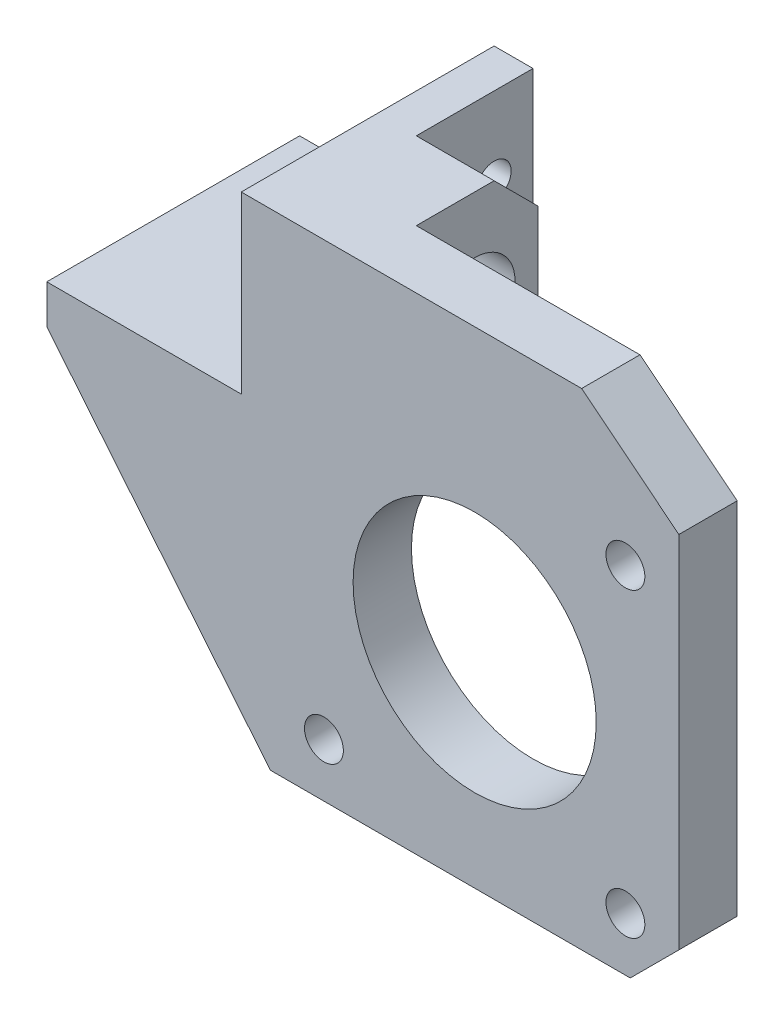
SolidWorks part; units mm, degrees
ref_plane "Plano frontal" through (0, 0, 0) normal (0, 0, 1) x (1, 0, 0)
ref_plane "Plano superior" through (0, 0, 0) normal (0, 1, 0) x (1, 0, 0)
ref_plane "Plano direito" through (0, 0, 0) normal (1, 0, 0) x (0, 0, -1)
sketch "Esboço1" plane through (0, 0, 0) normal (0, 0, 1) x (1, 0, 0)
  line L3 (-49.7252, 0) -> (0, 0) construction
  line L18 (-15.5, 15.5) -> (15.5, -15.5) construction
  line L19 (-15.5, -15.5) -> (15.5, 15.5) construction
  line L20 (15.5, -15.5) -> (15.5, 15.5) construction
  line L21 (-15.5, 15.5) -> (15.5, 15.5) construction
  line L22 (-15.5, -15.5) -> (-15.5, 15.5) construction
  line L23 (-15.5, -15.5) -> (15.5, -15.5) construction
  line L26 (-44, 7) -> (-21, -21)
  line L27 (11, 29) -> (21, 21)
  line L28 (-24, 29) -> (11, 29)
  line L29 (-24, 21) -> (-24, 29)
  line L30 (-44, 11) -> (-44, 7)
  line L31 (21, -21) -> (21, 21)
  line L32 (-24, 11) -> (-24, 21)
  line L33 (-21, -21) -> (21, -21)
  line L34 (-24, 11) -> (-44, 11)
  circle A3 centre (0, 0) radius 12.5
  circle A4 centre (15.5, 15.5) radius 2
  circle A5 centre (15.5, -15.5) radius 2
  circle A6 centre (-15.5, -15.5) radius 2
  point P0 (0, 0)
  point P1 (-21, 21)
  point P2 (-21, -21)
  point P3 (0, -15.5)
  point P4 (15.5, 0)
  point P6 (0, 0)
  point P7 (0, 0)
  point P8 (-21, -21)
  point P9 (0, 0)
  dimension "D2" = 42
  dimension "D5" = 25
  dimension "D3" = 4
  dimension "D1" = 31
  dimension "D4" = 8
  dimension "D6" = 10
  dimension "D7" = 21
  dimension "D8" = 20
  dimension "D9" = 18
  dimension "D10" = 28
  dimension "D11" = 24
extrude "Ressalto-extrusão1" add sketch "Esboço1" along normal blind 6
sketch "Esboço2" plane through (0, 0, 0) normal (0, 0, -1) x (-1, 0, 0)
  line L0 (44, 11) -> (44, 7)
  line L1 (44, 7) -> (24, 7)
  line L2 (20, 11) -> (20, 29)
  line L3 (-11, 29) -> (24, 29) construction
  line L4 (20, 29) -> (24, 29)
  line L5 (24, 29) -> (24, 11)
  line L6 (24, 11) -> (44, 11)
  line L7 (24, 11) -> (44, 11) construction
  line L8 (44, 11) -> (44, 7) construction
  line L9 (44, 7) -> (21, -21) construction
  line L10 (24, 29) -> (24, 11) construction
  arc A0 (20, 11) -> (24, 7) centre (24, 11) ccw
extrude "Ressalto-extrusão2" add sketch "Esboço2" along normal blind 20
sketch "Esboço3" plane through (-20, 0, 0) normal (1, 0, 0) x (0, 0, -1)
  line L0 (0, 29) -> (8, 29)
  line L2 (8, 29) -> (12.5, 24.5)
  line L3 (12.5, 24.5) -> (12.5, 13.5)
  line L4 (12.5, 13.5) -> (8, 9)
  line L5 (20, 29) -> (0, 29) construction
  line L6 (8, 9) -> (0, 9)
  line L7 (0, 9) -> (0, 29)
  line L9 (8, 29) -> (8, 9) construction
  line L10 (0, 29) -> (0, 11) construction
  circle A0 centre (6, 19) radius 4.15
  point P6 (12.5, 19)
  dimension "D1" = 8.3
  dimension "D2" = 6
  dimension "D3" = 20
  dimension "D4" = 11
  dimension "D5" = 2
extrude "Ressalto-extrusão3" add sketch "Esboço3" along normal blind 8
sketch "Esboço5" plane through (-20, 0, 0) normal (1, 0, 0) x (0, 0, -1)
  line L1 (20, 11) -> (20, 29) construction
  line L2 (20, 11) -> (10, 11) construction
  circle A0 centre (16, 21) radius 1.75
  circle A2 centre (6, 19) radius 4.15
  dimension "D3" = 3.5
  dimension "D1" = 10
  dimension "D2" = 4
extrude "Corte-extrusão2" cut sketch "Esboço5" against normal blind 12
sketch "Esboço6" plane through (0, 7, 0) normal (0, -1, 0) x (-1, 0, 0)
  line L1 (24, 20) -> (44, 20) construction
  line L2 (24, 20) -> (24, 0) construction
  circle A0 centre (34.5, 13) radius 1.75
  point P2 (31.5, 13)
  dimension "D1" = 3.5
  dimension "D3" = 10.5
  dimension "D4" = 7
extrude "Corte-extrusão3" cut sketch "Esboço6" against normal blind 12
chamfer "Chanfro1" distance 5 angle 45 1 edges at (21, -21, 3)
sketch "Esboço8" plane through (-24, 0, 0) normal (-1, 0, 0) x (0, 0, 1)
  circle A0 centre (-16, 21) radius 5.25
  dimension "D1" = 10.5
extrude "Corte-extrusão5" cut sketch "Esboço8" against normal blind 1
sketch "Esboço9" plane through (0, 11, 0) normal (0, 1, 0) x (1, 0, 0)
  circle A0 centre (-34.5, 13) radius 5.25
  dimension "D1" = 10.5
extrude "Corte-extrusão6" cut sketch "Esboço9" against normal blind 1
